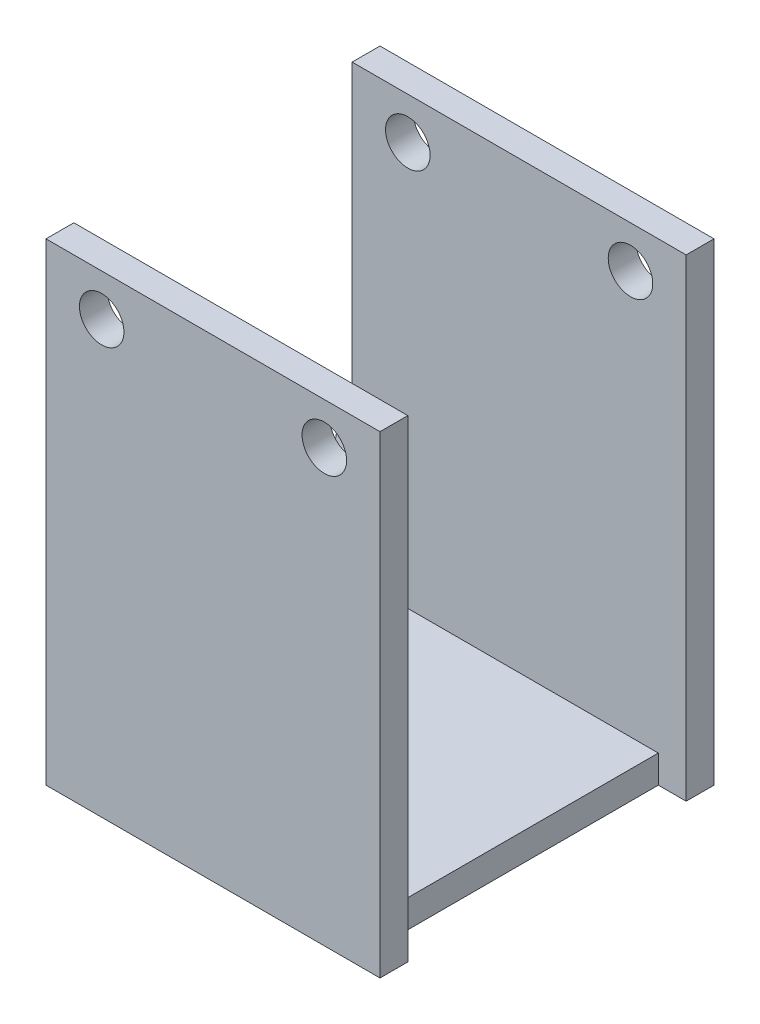
SolidWorks part; units mm, degrees
material "6061 合金"
ref_plane "前视基准面" through (0, 0, 0) normal (0, 0, 1) x (1, 0, 0)
ref_plane "上视基准面" through (0, 0, 0) normal (0, 1, 0) x (1, 0, 0)
ref_plane "右视基准面" through (0, 0, 0) normal (1, 0, 0) x (0, 0, -1)
sketch "草图1" plane through (0, 0, 0) normal (0, 1, 0) x (1, 0, 0)
  line L1 (0, 0) -> (10, 0)
  line L2 (0, 0) -> (0, 10)
  line L3 (0, 10) -> (10, 10)
  line L4 (10, 0) -> (10, 10)
  dimension "D1" = 10
  dimension "D2" = 10
extrude "凸台-拉伸1" add sketch "草图1" along normal blind 1
sketch "草图2" plane through (0, 0, 0) normal (-1, 0, 0) x (0, 0, 1)
  line L0 (-9.5, 6.5) -> (-10, 6.5)
  line L1 (0, 0) -> (-10, 0)
  line L2 (0, 0) -> (0, 6.5)
  line L3 (0, 6.5) -> (-0.5, 6.5)
  line L4 (-10, 0) -> (-10, 6.5)
  line L5 (-5, 0) -> (-5, 7.9037) construction
  arc A0 (-9.5, 6.5) -> (-0.5, 6.5) centre (-5, 6.5) ccw
  dimension "D3" = 4.5
  dimension "D1" = 10
  dimension "D2" = 6.5
extrude "凸台-拉伸2" add sketch "草图2" along normal blind 1
sketch "草图4" plane through (0, 0, 0) normal (0, 0, 1) x (1, 0, 0)
  line L1 (-1, 0) -> (11, 0)
  line L2 (-1, 0) -> (-1, 17)
  line L3 (-1, 17) -> (11, 17)
  line L4 (11, 0) -> (11, 17)
  dimension "D1" = 12
  dimension "D2" = 17
extrude "凸台-拉伸4" add sketch "草图4" along normal blind 1
sketch "草图5" plane through (0, 0, -10) normal (0, 0, -1) x (-1, 0, 0)
  line L4 (-11, 0) -> (1, 0)
  line L5 (-11, 17) -> (-11, 0)
  line L6 (1, 17) -> (-11, 17)
  line L7 (1, 0) -> (1, 17)
  line L8 (-11, 0) -> (1, 0)
  line L9 (-11, 17) -> (-11, 0)
  line L10 (1, 17) -> (-11, 17)
  line L11 (1, 0) -> (1, 17)
  dimension "D1" = 0
extrude "凸台-拉伸5" add sketch "草图5" along normal blind 1
hole_wizard "M2 螺纹孔1" positions "草图7" profile "草图6" tap size "M2" standard "Gb"
sketch "草图7" plane through (0, 0, -11) normal (0, 0, -1) x (-1, 0, 0)
  line L0 (-11, 15.5) -> (1, 15.5) construction
  line L1 (-11, 17) -> (-11, 0) construction
  line L2 (1, 0) -> (1, 17) construction
  line L7 (1, 17) -> (-11, 17) construction
  line L12 (-5, 0) -> (-5, 17) construction
  line L13 (-11, 0) -> (1, 0) construction
  line L14 (1, 17) -> (-11, 17) construction
  point P2 (-9, 15.5)
  point P50 (-1, 15.5)
  dimension "D1" = 1.5
  dimension "D2" = 2
  dimension "D3" = 8
cosmetic thread "孔螺蚊线2" parameters "D1"=4, "D2"=2
sketch "草图6" plane through (9, 15.5, -11) normal (1, 0, 0) x (0, 1, 0)
  line L0 (0, 0) -> (0, 12.4797)
  line L1 (0, 12.4797) -> (0.8, 11.999)
  line L2 (0.8, 11.999) -> (0.8, 0)
  line L5 (0.8, 0) -> (0, 0)
  line L10 (0, 12.4797) -> (-0.8, 11.999) construction
  line L11 (0, -6.35) -> (0, 107.95) construction
  dimension "螺纹孔钻头直径" = 1.6
  dimension "螺纹孔钻头深度" = 11.999
  dimension "导头角度" = 118
cosmetic thread "孔螺蚊线3" parameters "D1"=4, "D2"=2
